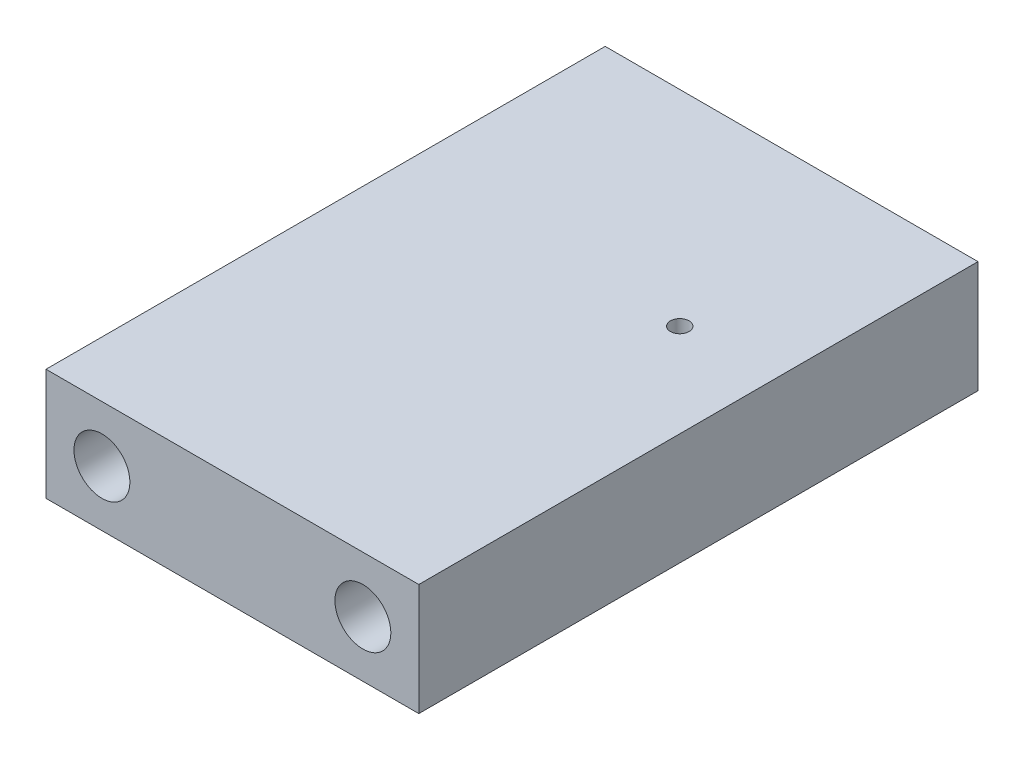
SolidWorks part; units mm, degrees
ref_plane "Alzado" through (0, 0, 0) normal (0, 0, 1) x (1, 0, 0)
ref_plane "Planta" through (0, 0, 0) normal (0, 1, 0) x (1, 0, 0)
ref_plane "Vista lateral" through (0, 0, 0) normal (1, 0, 0) x (0, 0, -1)
sketch "Croquis1" plane through (0, 0, 0) normal (0, 0, 1) x (1, 0, 0)
  line L1 (0, 0) -> (20, 0)
  line L2 (0, 0) -> (0, 6)
  line L3 (0, 6) -> (20, 6)
  line L4 (20, 0) -> (20, 6)
  dimension "D1" = 6
  dimension "D2" = 20
extrude "Saliente-Extruir1" add sketch "Croquis1" along normal blind 30
sketch "Croquis2" plane through (0, 0, 30) normal (0, 0, 1) x (1, 0, 0)
  line L0 (0, 3) -> (20, 3) construction
  line L1 (0, 6) -> (0, 0) construction
  line L2 (20, 0) -> (20, 6) construction
  circle A0 centre (3, 3) radius 1.5
  circle A1 centre (17, 3) radius 1.5
  dimension "D1" = 3
  dimension "D2" = 3
  dimension "D3" = 14
  dimension "D4" = 3
extrude "Cortar-Extruir1" cut sketch "Croquis2" against normal blind 5
sketch "Croquis3" plane through (0, 0, 0) normal (0, 0, -1) x (-1, 0, 0)
  circle A1 centre (-17, 3) radius 1.5
  circle A2 centre (-17, 3) radius 1.5
  circle A3 centre (-3, 3) radius 1.5
  circle A4 centre (-3, 3) radius 1.5
  dimension "D1" = 0
  dimension "D2" = 0
extrude "Cortar-Extruir3" cut sketch "Croquis3" against normal blind 5
sketch "Croquis4" plane through (0, 6, 0) normal (0, 1, 0) x (1, 0, 0)
  line L1 (0, -30) -> (0, 0) construction
  line L2 (20, 0) -> (0, 0) construction
  circle A0 centre (15, -11) radius 0.5
  dimension "D1" = 1
  dimension "D2" = 11
  dimension "D3" = 15
extrude "Cortar-Extruir4" cut sketch "Croquis4" against normal blind 10
